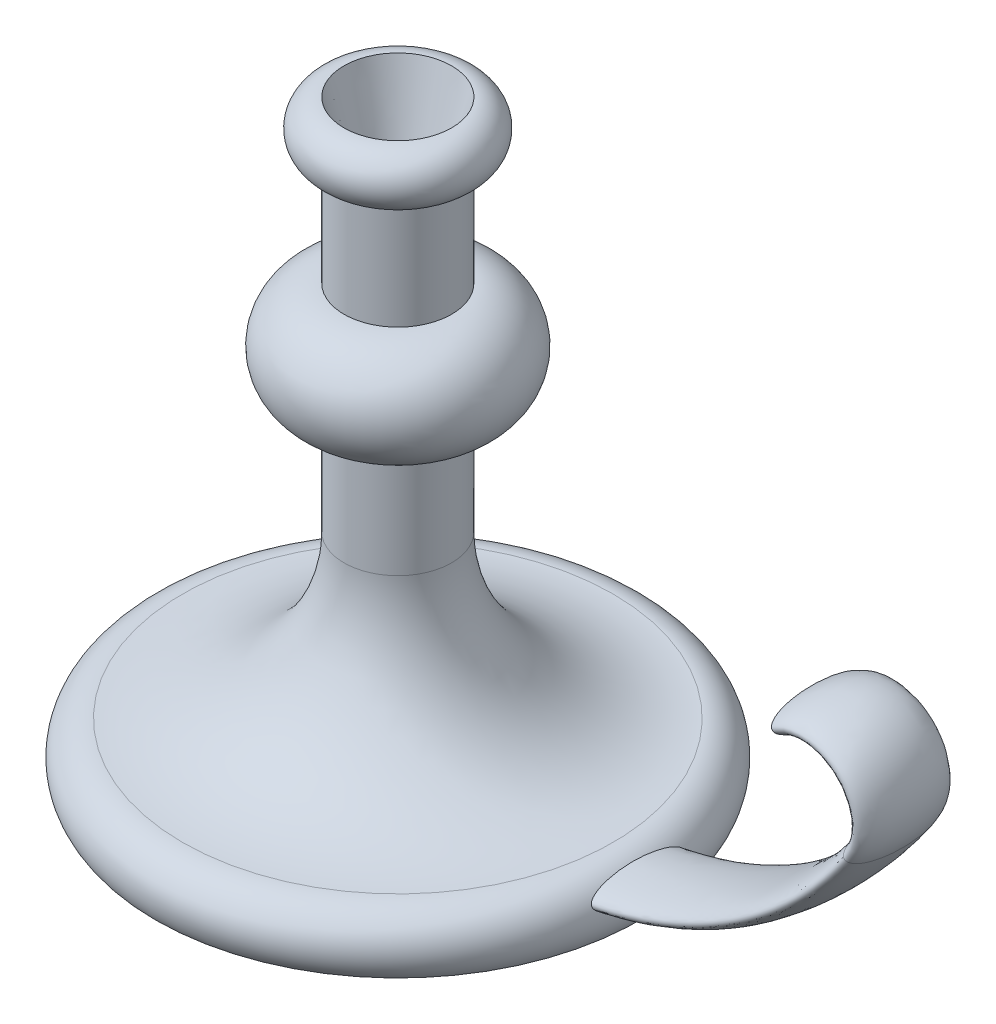
SolidWorks part; units mm, degrees
ref_plane "Front Plane" through (0, 0, 0) normal (0, 0, 1) x (1, 0, 0)
ref_plane "Top Plane" through (0, 0, 0) normal (0, 1, 0) x (1, 0, 0)
ref_plane "Right Plane" through (0, 0, 0) normal (1, 0, 0) x (0, 0, -1)
sketch "Sketch1" plane through (0, 0, 0) normal (0, 0, 1) x (1, 0, 0)
  line L0 (0, 0) -> (0, 220)
  line L1 (0, 220) -> (20, 220)
  line L2 (0, 0) -> (90, 0)
  line L3 (20, 200) -> (20, 160)
  line L4 (20, 120) -> (20, 80)
  arc A0 (20, 220) -> (20, 200) centre (20, 210) cw
  arc A1 (20, 160) -> (20, 120) centre (20, 140) cw
  arc A2 (20, 80) -> (80, 20) centre (80, 80) ccw
  arc A3 (80, 20) -> (90, 0) centre (80, 7.5) cw
  dimension "D4" = 10
  dimension "D5" = 40
  dimension "D6" = 20
  dimension "D7" = 60
  dimension "D8" = 12.5
  dimension "D1" = 20
  dimension "D2" = 220
  dimension "D3" = 90
  dimension "D9" = 80
revolve "Revolve1" add sketch "Sketch1" angle 360 about L0
sketch "Sketch2" plane through (0, 0, 0) normal (1, 0, 0) x (0, 0, -1)
  line L0 (0, 0) -> (0, 10) construction
  line L2 (-90, 0) -> (90, 0) construction
  ellipse E1 centre (0, 10) end of major axis (17.5, 10) minor radius 5
  dimension "D1" = 35
  dimension "D2" = 10
  dimension "D3" = 10
sketch "Sketch3" plane through (0, 0, 0) normal (0, 0, 1) x (1, 0, 0)
  line L0 (0, 10) -> (60, 10)
  line L1 (0, 164) -> (0, 92) construction
  line L2 (0, 0) -> (0, 10) construction
  line L3 (-90, 0) -> (90, 0) construction
  arc A0 (60, 10) -> (183.5921, 75) centre (60, 160) ccw
  arc A1 (183.5921, 75) -> (156.5808, 103.3354) centre (167.1131, 86.3333) ccw
  dimension "D3" = 150
  dimension "D4" = 20
  dimension "D1" = 60
  dimension "D2" = 65
  dimension "D5" = 10
sweep "Sweep1" add profiles "Sketch2" path "Sketch3"
sketch "Sketch4" plane through (0, 220, 0) normal (0, 1, 0) x (1, 0, 0)
  circle A0 centre (0, 0) radius 20
extrude "Cut-Extrude1" cut sketch "Sketch4" against normal blind 25 draft 15
